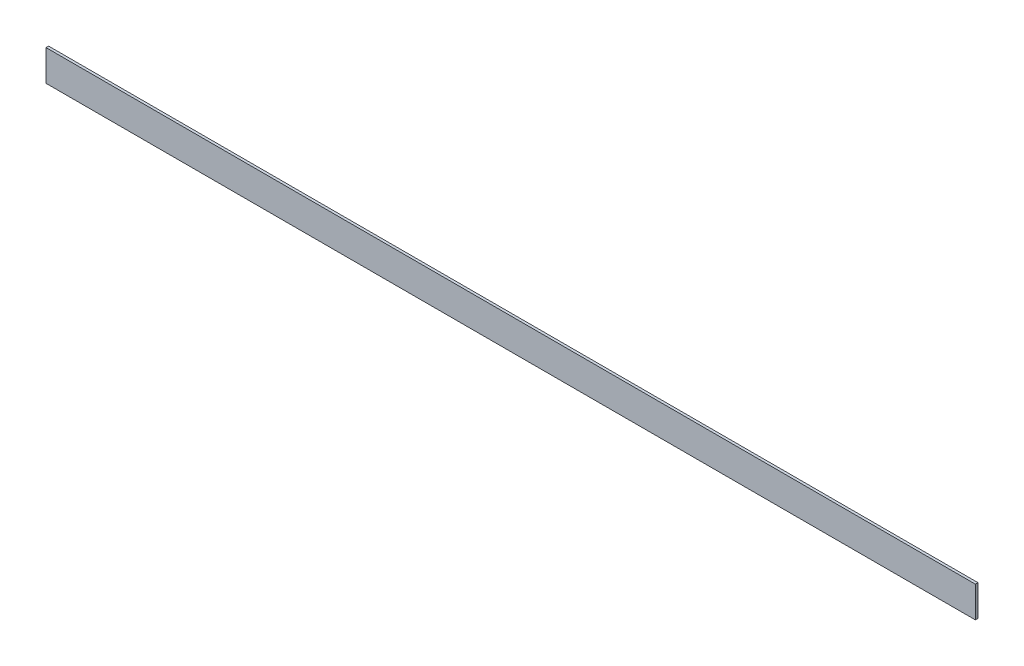
SolidWorks part; units mm, degrees
material "PVC 0.007 Plasticized"
ref_plane "Front Plane" through (0, 0, 0) normal (0, 0, 1) x (1, 0, 0)
ref_plane "Top Plane" through (0, 0, 0) normal (0, 1, 0) x (1, 0, 0)
ref_plane "Right Plane" through (0, 0, 0) normal (1, 0, 0) x (0, 0, -1)
sketch "Sketch1" plane through (0, 0, 0) normal (1, 0, 0) x (0, 0, -1)
  line L1 (-3.175, -38.1) -> (3.175, -38.1)
  line L2 (-3.175, -38.1) -> (-3.175, 38.1)
  line L3 (-3.175, 38.1) -> (3.175, 38.1)
  line L4 (3.175, -38.1) -> (3.175, 38.1)
  line L5 (-3.175, -38.1) -> (3.175, 38.1) construction
  line L6 (-3.175, 38.1) -> (3.175, -38.1) construction
  point P0 (0, 0)
  dimension "D1" = 76.2
  dimension "D2" = 6.35
extrude "Boss-Extrude1" add sketch "Sketch1" along normal blind 2286
equation "\"D2@Sketch1\"=1in/4"
